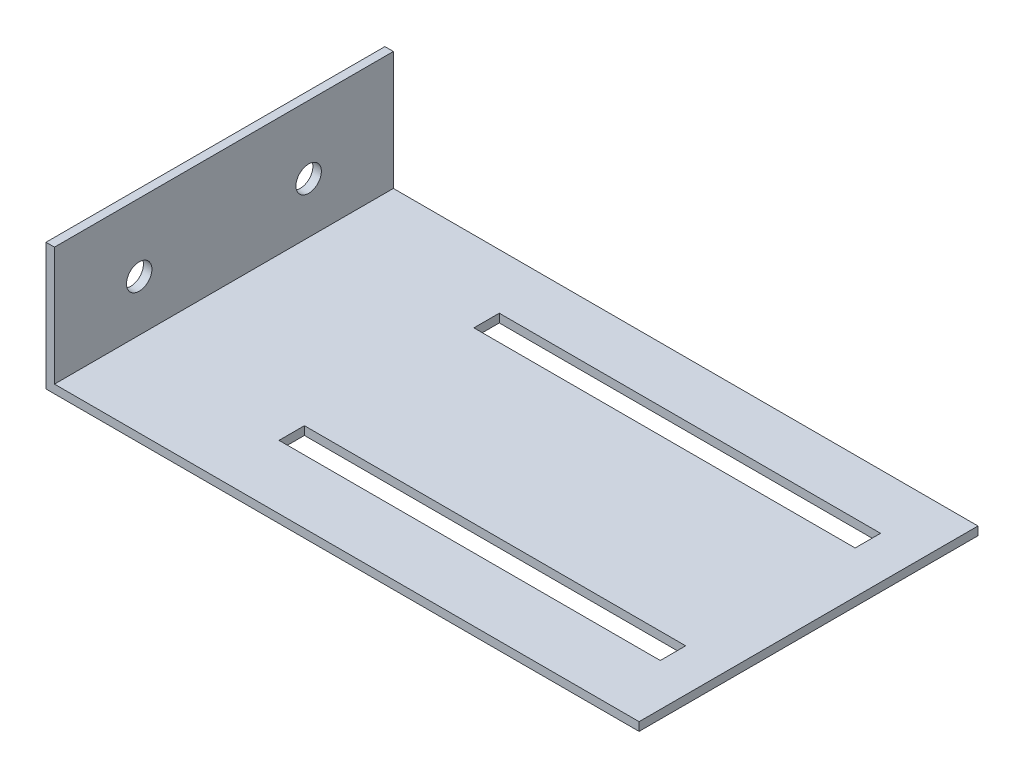
SolidWorks part; units mm, degrees
ref_plane "Front Plane" through (0, 0, 0) normal (0, 0, 1) x (1, 0, 0)
ref_plane "Top Plane" through (0, 0, 0) normal (0, 1, 0) x (1, 0, 0)
ref_plane "Right Plane" through (0, 0, 0) normal (1, 0, 0) x (0, 0, -1)
sketch "Sketch1" plane through (0, 0, 0) normal (0, 0, 1) x (1, 0, 0)
  line L0 (0, 0) -> (70, 0)
  line L1 (70, 0) -> (70, 1)
  line L2 (70, 1) -> (1, 1)
  line L3 (1, 1) -> (1, 15)
  line L4 (1, 15) -> (0, 15)
  line L5 (0, 15) -> (0, 0)
  dimension "D1" = 69
  dimension "D2" = 1
  dimension "D3" = 14
  dimension "D4" = 1
  dimension "D5" = 15
  dimension "D6" = 70
extrude "Boss-Extrude1" add sketch "Sketch1" along normal blind 40
sketch "Sketch2" plane through (0, 1, 0) normal (0, 1, 0) x (1, 0, 0)
  line L0 (70, -40) -> (70, 0) construction
  line L1 (20, -6.5) -> (65, -6.5)
  line L2 (20, -6.5) -> (20, -9.5)
  line L3 (20, -9.5) -> (65, -9.5)
  line L4 (65, -6.5) -> (65, -9.5)
  line L5 (70, 0) -> (1, 0) construction
  line L6 (20, -32.5) -> (65, -32.5)
  line L7 (20, -32.5) -> (20, -29.5)
  line L8 (20, -29.5) -> (65, -29.5)
  line L9 (65, -32.5) -> (65, -29.5)
  point P10 (20, -8)
  point P11 (20, -31)
  dimension "D1" = 3
  dimension "D2" = 45
  dimension "D3" = 5
  dimension "D4" = 3
  dimension "D5" = 45
  dimension "D6" = 23
  dimension "D7" = 5
  dimension "D8" = 8
extrude "Cut-Extrude1" cut sketch "Sketch2" against normal blind 10
sketch "Sketch3" plane through (0, 0, 0) normal (-1, 0, 0) x (0, 0, 1)
  line L0 (0, 15) -> (0, 0) construction
  line L1 (40, 15) -> (40, 0) construction
  line L2 (40, 0) -> (0, 0) construction
  circle A0 centre (30, 7) radius 1.5
  circle A1 centre (10, 7) radius 1.5
  dimension "D1" = 3
  dimension "D2" = 3
  dimension "D4" = 10
  dimension "D5" = 7
  dimension "D6" = 3
  dimension "D7" = 7
  dimension "D3" = 10
extrude "Cut-Extrude2" cut sketch "Sketch3" against normal blind 10
